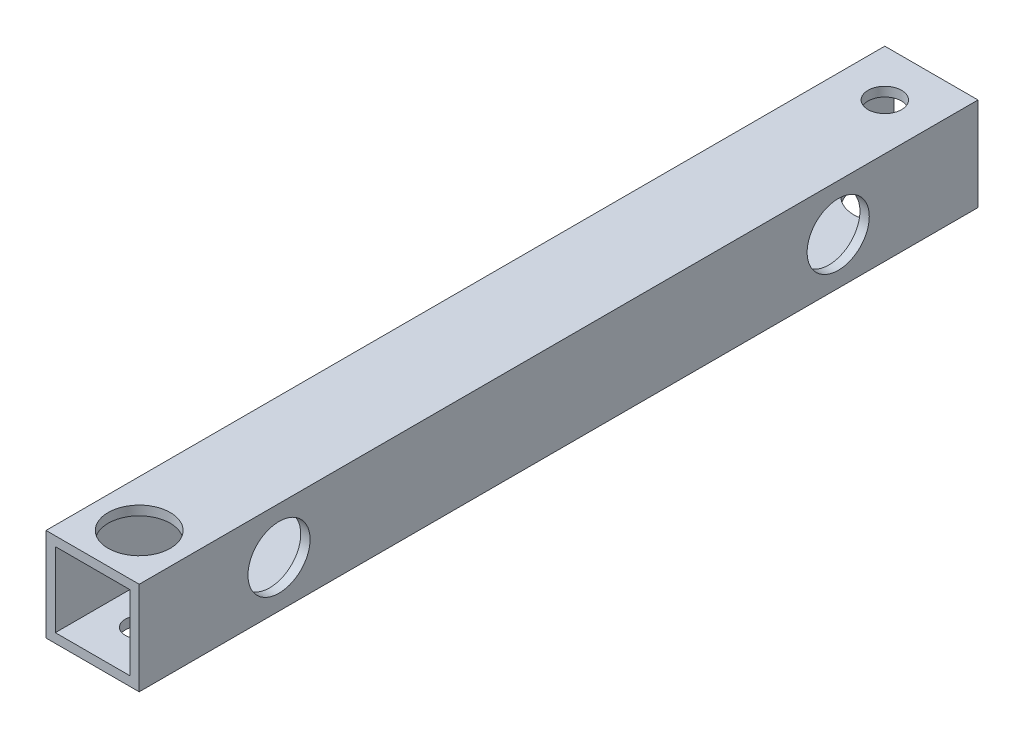
SolidWorks part; units mm, degrees
material "6063-T5"
ref_plane "正面" through (0, 0, 0) normal (0, 0, 1) x (1, 0, 0)
ref_plane "平面" through (0, 0, 0) normal (0, 1, 0) x (1, 0, 0)
ref_plane "右側面" through (0, 0, 0) normal (1, 0, 0) x (0, 0, -1)
sketch "ｽｹｯﾁ1" plane through (0, 0, 0) normal (0, 0, 1) x (1, 0, 0)
  line L1 (-7.5, -7.5) -> (7.5, -7.5)
  line L2 (-7.5, -7.5) -> (-7.5, 7.5)
  line L3 (-7.5, 7.5) -> (7.5, 7.5)
  line L4 (7.5, -7.5) -> (7.5, 7.5)
  line L5 (-7.5, -7.5) -> (7.5, 7.5) construction
  line L6 (-7.5, 7.5) -> (7.5, -7.5) construction
  line L7 (-6, -6) -> (6, -6)
  line L8 (-6, -6) -> (-6, 6)
  line L9 (-6, 6) -> (6, 6)
  line L10 (6, -6) -> (6, 6)
  line L11 (-6, -6) -> (6, 6) construction
  line L12 (-6, 6) -> (6, -6) construction
  point P0 (0, 0)
  point P6 (0, 0)
  dimension "D1" = 1.5
  dimension "D2" = 15
  dimension "D3" = 15
extrude "ﾎﾞｽ - 押し出し1" add sketch "ｽｹｯﾁ1" along normal blind 135
sketch "ｽｹｯﾁ2" plane through (7.5, 0, 0) normal (1, 0, 0) x (0, 0, -1)
  line L0 (-135, -7.5) -> (0, -7.5) construction
  line L2 (-135, -7.5) -> (-135, 7.5) construction
  circle A4 centre (-112.5, 0) radius 2.7
  circle A8 centre (-22.5, 0) radius 2.7
  dimension "D1" = 5.4
  dimension "D2" = 22.5
  dimension "D3" = 7.5
  dimension "D4" = 90
  dimension "D9" = 2
extrude "ｶｯﾄ - 押し出し1" cut sketch "ｽｹｯﾁ2" against normal blind 25
sketch "ｽｹｯﾁ3" plane through (0, 7.5, 0) normal (0, 1, 0) x (1, 0, 0)
  line L2 (7.5, -135) -> (7.5, 0) construction
  circle A1 centre (0, -7.5) radius 2.7
  circle A6 centre (0, -127.5) radius 2.25
  dimension "D2" = 120
  dimension "D3" = 5.4
  dimension "D9" = 7.5
  dimension "D11" = 7.5
  dimension "D4" = 7.5
  dimension "D5" = 4.5
extrude "ｶｯﾄ - 押し出し2" cut sketch "ｽｹｯﾁ3" against normal blind 25
sketch "ｽｹｯﾁ4" plane through (0, 7.5, 0) normal (0, 1, 0) x (1, 0, 0)
  circle A0 centre (0, -127.5) radius 5
  dimension "D2" = 10
extrude "ｶｯﾄ - 押し出し3" cut sketch "ｽｹｯﾁ4" against normal blind 10
sketch "ｽｹｯﾁ5" plane through (7.5, 0, 0) normal (1, 0, 0) x (0, 0, -1)
  circle A0 centre (-22.5, 0) radius 5
  circle A1 centre (-112.5, 0) radius 5
  dimension "D1" = 10
  dimension "D2" = 10
extrude "ｶｯﾄ - 押し出し4" cut sketch "ｽｹｯﾁ5" against normal blind 10
sketch "ｽｹｯﾁ6" plane through (0, -7.5, 0) normal (0, -1, 0) x (-1, 0, 0)
  circle A0 centre (0, -7.5) radius 5
  dimension "D1" = 10
extrude "ｶｯﾄ - 押し出し5" cut sketch "ｽｹｯﾁ6" against normal blind 10
